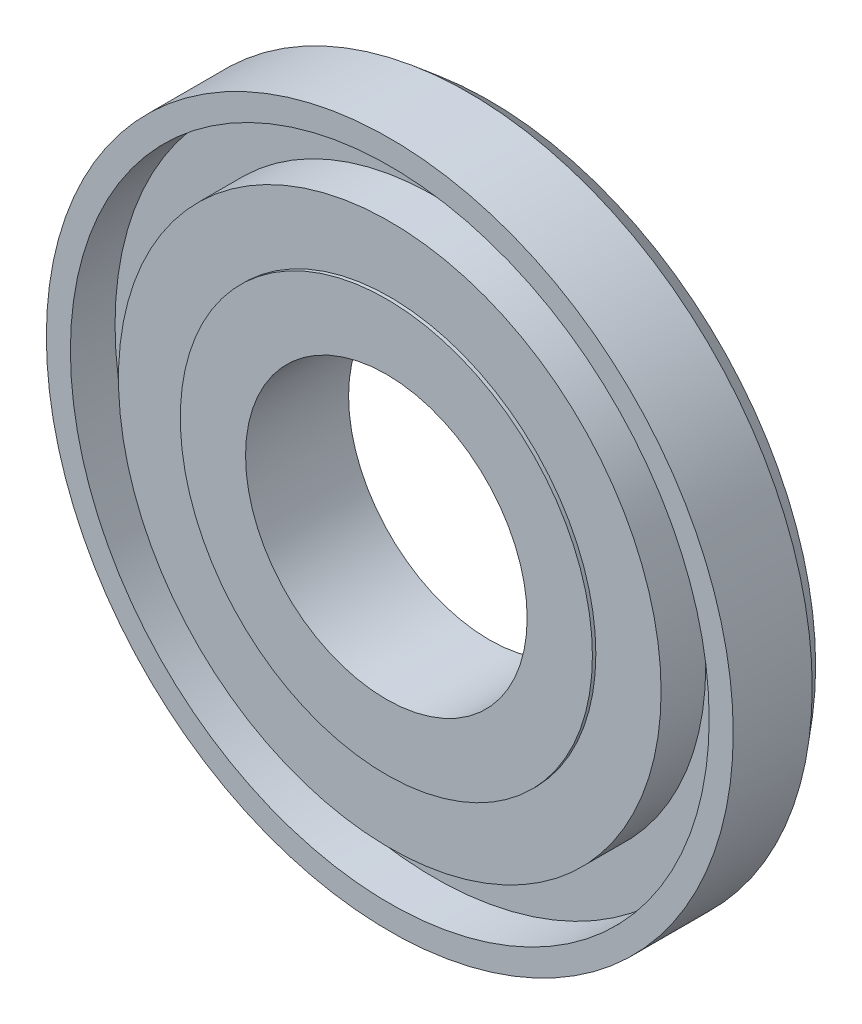
SolidWorks part; units mm, degrees
material "Acier S235"
ref_plane "Plan de face" through (0, 0, 0) normal (0, 0, 1) x (1, 0, 0)
ref_plane "Plan de dessus" through (0, 0, 0) normal (0, 1, 0) x (1, 0, 0)
ref_plane "Plan de droite" through (0, 0, 0) normal (1, 0, 0) x (0, 0, -1)
sketch "Esquisse1" plane through (0, 0, 0) normal (0, 1, 0) x (1, 0, 0)
  line L0 (39.5, -8) -> (46.5, -8)
  line L1 (46.5, -8) -> (46.5, -14.5)
  line L2 (46.5, -14.5) -> (50, -14.5)
  line L3 (50, -14.5) -> (50, -3)
  line L4 (50, -3) -> (47.5, 0)
  line L5 (47.5, 0) -> (20.5, 0)
  line L6 (20.5, 0) -> (20.5, -15)
  line L7 (20.5, -15) -> (30, -15)
  line L8 (30, -15) -> (30, -14.5)
  line L9 (30, -14.5) -> (39.5, -14.5)
  line L10 (39.5, -14.5) -> (39.5, -8)
  line L11 (0, 0) -> (0, -15) construction
  dimension "D1" = 27
  dimension "D2" = 7
  dimension "D3" = 3.5
  dimension "D4" = 9.5
  dimension "D5" = 9.5
  dimension "D6" = 15
  dimension "D7" = 11.5
  dimension "D8" = 3
revolve "Révolution1" add sketch "Esquisse1" angle 360 about L11
